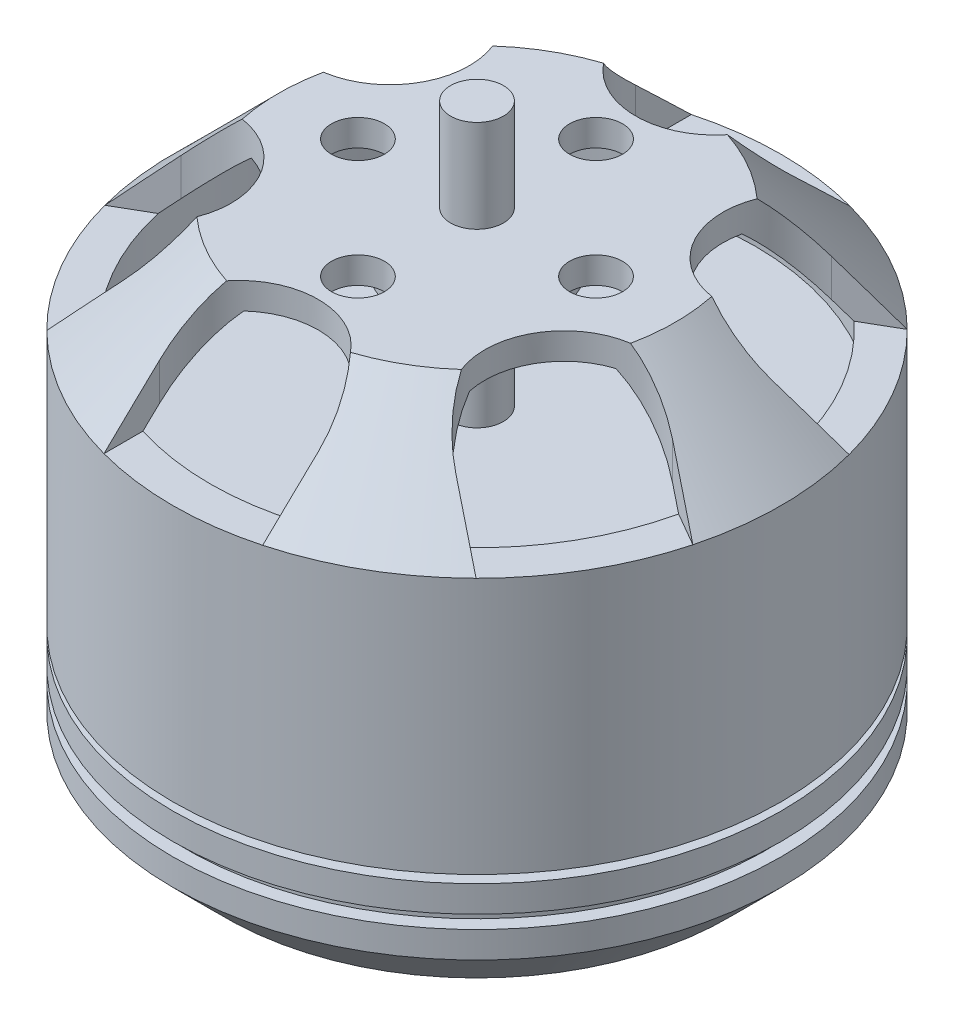
SolidWorks part; units mm, degrees
ref_plane "Front Plane" through (0, 0, 0) normal (0, 0, 1) x (1, 0, 0)
ref_plane "Top Plane" through (0, 0, 0) normal (0, 1, 0) x (1, 0, 0)
ref_plane "Right Plane" through (0, 0, 0) normal (1, 0, 0) x (0, 0, -1)
sketch "Sketch1" plane through (0, 0, 0) normal (0, 0, 1) x (1, 0, 0)
  line L0 (0, 0) -> (0, 21.2819)
  line L1 (1, -0.7181) -> (9.5, -0.7181)
  line L2 (9.5, -0.7181) -> (11.5, 1.2819)
  line L3 (11.5, 1.2819) -> (11.5, 2.2819)
  line L4 (11.5, 13.7819) -> (7.5, 17.7819)
  line L5 (7.5, 17.7819) -> (1, 17.7819)
  line L6 (1, 17.7819) -> (1, 21.2819)
  line L7 (1, 21.2819) -> (0, 21.2819)
  line L8 (2.9004, 16.7819) -> (7.0858, 16.7819)
  line L9 (7.0858, 16.7819) -> (10.5, 13.3677)
  line L10 (0, 0) -> (0, -2.5181)
  line L11 (0, -2.5181) -> (1, -2.5181)
  line L12 (1, -0.7181) -> (1, -2.5181)
  line L13 (10.5, 13.3677) -> (10.5, 11.2813)
  line L14 (10.5, 11.2813) -> (1, 11.2813)
  line L15 (1, 11.2813) -> (1, 15.7819)
  line L16 (1, 15.7819) -> (2.9004, 15.7819)
  line L17 (2.9004, 15.7819) -> (2.9004, 16.7819)
  line L18 (11.5, 2.7819) -> (11.5, 3.7819)
  line L19 (11.5, 2.7819) -> (11, 2.7819)
  line L20 (11.5, 4.0819) -> (11.5, 13.7819)
  line L21 (11.5, 2.2819) -> (11, 2.2819)
  line L22 (11, 2.7819) -> (11, 2.2819)
  line L23 (11.5, 4.0819) -> (9.5, 4.0819)
  line L25 (11.5, 3.7819) -> (9.5, 3.7819)
  line L26 (9.5, 4.0819) -> (9.5, 3.7819)
  dimension "D1" = 23.8
  dimension "D2" = 1.8
  dimension "D3" = 45
  dimension "D4" = 2
  dimension "D5" = 11.5
  dimension "D6" = 1
  dimension "D7" = 1
  dimension "D8" = 3.5
  dimension "D9" = 45
  dimension "D10" = 1
  dimension "D11" = 1
  dimension "D12" = 1
  dimension "D13" = 1
  dimension "D14" = 4
  dimension "D15" = 0.5
  dimension "D16" = 0.5
  dimension "D17" = 1
  dimension "D18" = 2
  dimension "D19" = 0.3
  dimension "D20" = 1
revolve "Revolve1" add sketch "Sketch1" angle 360 about L0
sketch "Sketch2" plane through (0, 17.7819, 0) normal (0, 1, 0) x (1, 0, 0)
  line L0 (0, 0) -> (0, 9) construction
  line L1 (9.2942, 1.9019) -> (15.7026, 5.6018)
  line L2 (12.7026, 10.7979) -> (15.7026, 5.6018)
  line L3 (-3, 9) -> (-3, 16.3997)
  line L4 (-3, 16.3997) -> (3, 16.3997)
  line L5 (3, 9) -> (3, 16.3997)
  line L6 (6.2942, 7.0981) -> (12.7026, 10.7979)
  line L7 (6.2942, -7.0981) -> (12.7026, -10.7979)
  line L8 (15.7026, -5.6018) -> (12.7026, -10.7979)
  line L9 (9.2942, -1.9019) -> (15.7026, -5.6018)
  line L10 (-3, -9) -> (-3, -16.3997)
  line L11 (3, -16.3997) -> (-3, -16.3997)
  line L12 (3, -9) -> (3, -16.3997)
  line L13 (-9.2942, -1.9019) -> (-15.7026, -5.6018)
  line L14 (-12.7026, -10.7979) -> (-15.7026, -5.6018)
  line L15 (-6.2942, -7.0981) -> (-12.7026, -10.7979)
  line L16 (-6.2942, 7.0981) -> (-12.7026, 10.7979)
  line L17 (-15.7026, 5.6018) -> (-12.7026, 10.7979)
  line L18 (-9.2942, 1.9019) -> (-15.7026, 5.6018)
  circle A0 centre (0, 0) radius 4.5 construction
  circle A1 centre (0, 0) radius 9.2287 construction
  circle A2 centre (0, -4.5) radius 1
  circle A3 centre (-4.5, 0) radius 1
  circle A4 centre (0, 4.5) radius 1
  circle A5 centre (4.5, 0) radius 1
  arc A6 (-3, 9) -> (3, 9) centre (0, 9) ccw
  arc A7 (6.2942, 7.0981) -> (9.2942, 1.9019) centre (7.7942, 4.5) ccw
  arc A8 (9.2942, -1.9019) -> (6.2942, -7.0981) centre (7.7942, -4.5) ccw
  arc A9 (3, -9) -> (-3, -9) centre (0, -9) ccw
  arc A10 (-6.2942, -7.0981) -> (-9.2942, -1.9019) centre (-7.7942, -4.5) ccw
  arc A11 (-9.2942, 1.9019) -> (-6.2942, 7.0981) centre (-7.7942, 4.5) ccw
  point P16 (0, 0)
  point P45 (0, 0)
  dimension "D1" = 9
  dimension "D3" = 2
  dimension "D5" = 6
  dimension "D2" = 9
  dimension "D4" = 4
  dimension "D6" = 6
extrude "Cut-Extrude1" cut sketch "Sketch2" against normal blind 4
sketch "Sketch3" plane through (0, -0.7181, 0) normal (0, -1, 0) x (1, 0, 0)
  circle A0 centre (0, 0) radius 6 construction
  circle A1 centre (0, 0) radius 8 construction
  circle A2 centre (8, 0) radius 1
  circle A3 centre (-8, 0) radius 1
  circle A4 centre (0, 6) radius 1
  circle A5 centre (0, -6) radius 1
  dimension "D1" = 16
  dimension "D2" = 12
  dimension "D3" = 2
extrude "Cut-Extrude2" cut sketch "Sketch3" against normal blind 3
